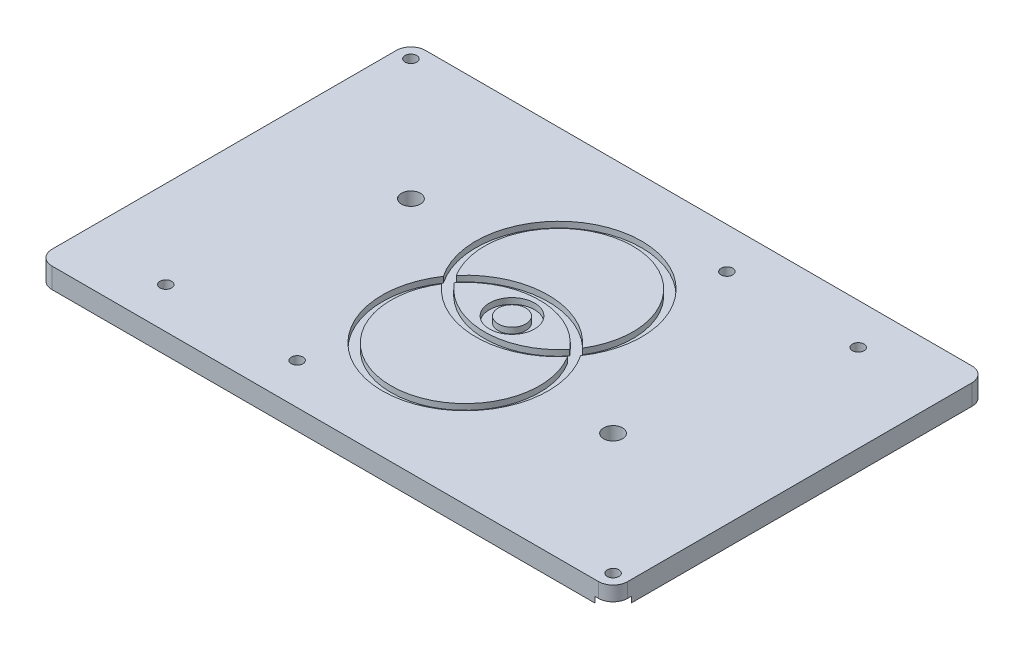
SolidWorks part; units mm, degrees
ref_plane "Front Plane" through (0, 0, 0) normal (0, 0, 1) x (1, 0, 0)
ref_plane "Top Plane" through (0, 0, 0) normal (0, 1, 0) x (1, 0, 0)
ref_plane "Right Plane" through (0, 0, 0) normal (1, 0, 0) x (0, 0, -1)
sketch "Sketch1" plane through (0, 0, 0) normal (0, 1, 0) x (1, 0, 0)
  line L0 (-98.1973, -11.2479) -> (-55.1973, 31.7521) construction
  line L1 (-118.1973, 56.7521) -> (69.0859, 56.7521)
  line L2 (-123.1973, 51.7521) -> (-123.1973, -66.2479)
  line L3 (-118.1973, -71.2479) -> (69.0859, -71.2479)
  line L4 (74.0859, 51.7521) -> (74.0859, -66.2479)
  line L5 (-98.1973, 31.7521) -> (-55.1973, 31.7521) construction
  line L6 (-98.1973, 31.7521) -> (-98.1973, -11.2479) construction
  line L7 (-98.1973, -11.2479) -> (-55.1973, -11.2479) construction
  line L8 (-55.1973, 31.7521) -> (-55.1973, -11.2479) construction
  line L9 (6.0859, -3.2479) -> (49.0859, -3.2479) construction
  line L10 (6.0859, -3.2479) -> (6.0859, -46.2479) construction
  line L11 (6.0859, -46.2479) -> (49.0859, -46.2479) construction
  line L12 (49.0859, -3.2479) -> (49.0859, -46.2479) construction
  line L13 (-76.6973, 60.2521) -> (119.5871, 60.2521) construction
  line L14 (6.0859, -46.2479) -> (49.0859, -3.2479) construction
  line L15 (27.5859, 25.2521) -> (119.5871, 25.2521) construction
  line L16 (-76.6973, -39.7479) -> (-210.8398, -39.7479) construction
  circle A0 centre (-76.6973, 10.2521) radius 50 construction
  circle A1 centre (27.5859, -24.7479) radius 50 construction
  circle A2 centre (-118.1973, 51.7521) radius 5 construction
  circle A3 centre (-118.1973, 51.7521) radius 2
  arc A4 (74.0859, 51.7521) -> (69.0859, 56.7521) centre (69.0859, 51.7521) ccw
  arc A5 (74.0859, -66.2479) -> (69.0859, -71.2479) centre (69.0859, -66.2479) cw
  arc A6 (-123.1973, -66.2479) -> (-118.1973, -71.2479) centre (-118.1973, -66.2479) ccw
  arc A7 (-123.1973, 51.7521) -> (-118.1973, 56.7521) centre (-118.1973, 51.7521) cw
  circle A8 centre (69.0859, -66.2479) radius 5 construction
  circle A9 centre (69.0859, -66.2479) radius 2
  circle A10 centre (-0.9141, 42.7521) radius 5 construction
  circle A11 centre (44.0859, 42.7521) radius 2
  circle A12 centre (-0.9141, 42.7521) radius 2
  circle A13 centre (44.0859, 42.7521) radius 5 construction
  circle A14 centre (-93.1973, -57.2479) radius 2
  circle A15 centre (-48.1973, -57.2479) radius 5 construction
  circle A16 centre (-48.1973, -57.2479) radius 2
  circle A17 centre (-93.1973, -57.2479) radius 5 construction
  circle A18 centre (-76.6973, 10.2521) radius 3.25
  circle A19 centre (27.5859, -24.7479) radius 3.25
  point P12 (27.5859, -24.7479)
  point P13 (-76.6973, 10.2521)
  dimension "D8" = 100
  dimension "D9" = 10
  dimension "D10" = 4
  dimension "D13" = 5
  dimension "D14" = 4
  dimension "D15" = 10
  dimension "D16" = 4
  dimension "D23" = 6.5
  dimension "D1" = 25
  dimension "D2" = 25
  dimension "D3" = 43
  dimension "D4" = 35
  dimension "D5" = 110
  dimension "D6" = 25
  dimension "D7" = 25
  dimension "D11" = 5
  dimension "D12" = 5
  dimension "D17" = 45
  dimension "D18" = 14
  dimension "D19" = 45
  dimension "D20" = 14
  dimension "D21" = 30
  dimension "D22" = 30
extrude "Boss-Extrude1" add sketch "Sketch1" along normal blind 7
sketch "Sketch2" plane through (0, 0, 0) normal (0, -1, 0) x (1, 0, 0)
  circle A0 centre (-118.1973, -51.7521) radius 5.15
  circle A1 centre (-0.9141, -42.7521) radius 5.15
  circle A2 centre (44.0859, -42.7521) radius 5.15
  circle A3 centre (69.0859, 66.2479) radius 5.15
  circle A4 centre (-48.1973, 57.2479) radius 5.15
  circle A5 centre (-93.1973, 57.2479) radius 5.15
  dimension "D1" = 10.3
extrude "Cut-Extrude1" cut sketch "Sketch2" against normal blind 2
sketch "Sketch4" plane through (0, 7, 0) normal (0, 1, 0) x (1, 0, 0)
  line L0 (-123.1973, 51.7521) -> (-123.1973, -66.2479) construction
  line L1 (69.0859, 56.7521) -> (-118.1973, 56.7521) construction
  line L2 (-118.1973, 51.7521) -> (69.0859, -66.2479) construction
  arc A3 (-48.0729, -7.2479) -> (-1.0385, -7.2479) centre (-24.5557, -23.2585) ccw
  arc A4 (-46.1388, -9.7728) -> (-2.9726, -9.7728) centre (-24.5557, 8.7626) ccw
  circle A5 centre (-24.5557, -7.2479) radius 7.7303
  arc A6 (-46.1388, -9.7728) -> (-2.9726, -9.7728) centre (-24.5557, -23.2585) ccw
  arc A7 (-44.3385, -7.2479) -> (-4.7729, -7.2479) centre (-24.5557, 8.7626) ccw
  circle A8 centre (-24.5557, -7.2479) radius 4.7303
  arc A15 (-4.7729, -7.2479) -> (-44.3385, -7.2479) centre (-24.5557, -23.2585) ccw
  arc A16 (-1.0385, -7.2479) -> (-48.0729, -7.2479) centre (-24.5557, 8.7626) ccw
  arc A17 (-2.9726, -4.723) -> (-46.1388, -4.723) centre (-24.5557, -23.2585) ccw
  arc A18 (-2.9726, -4.723) -> (-46.1388, -4.723) centre (-24.5557, 8.7626) ccw
  point P10 (-24.5557, -7.2479)
  dimension "D1" = 192.2833
  dimension "D3" = 5
  dimension "D2" = 5
extrude "Cut-Extrude3" cut sketch "Sketch4" against normal blind 2 contours L2 A5 A8 | A5 L2 A8 | A16 L2 A18 A17 A15 A7 A4 A6 A3 | L2 A16 A3 A6 A4 A7 A15 A17 A18
